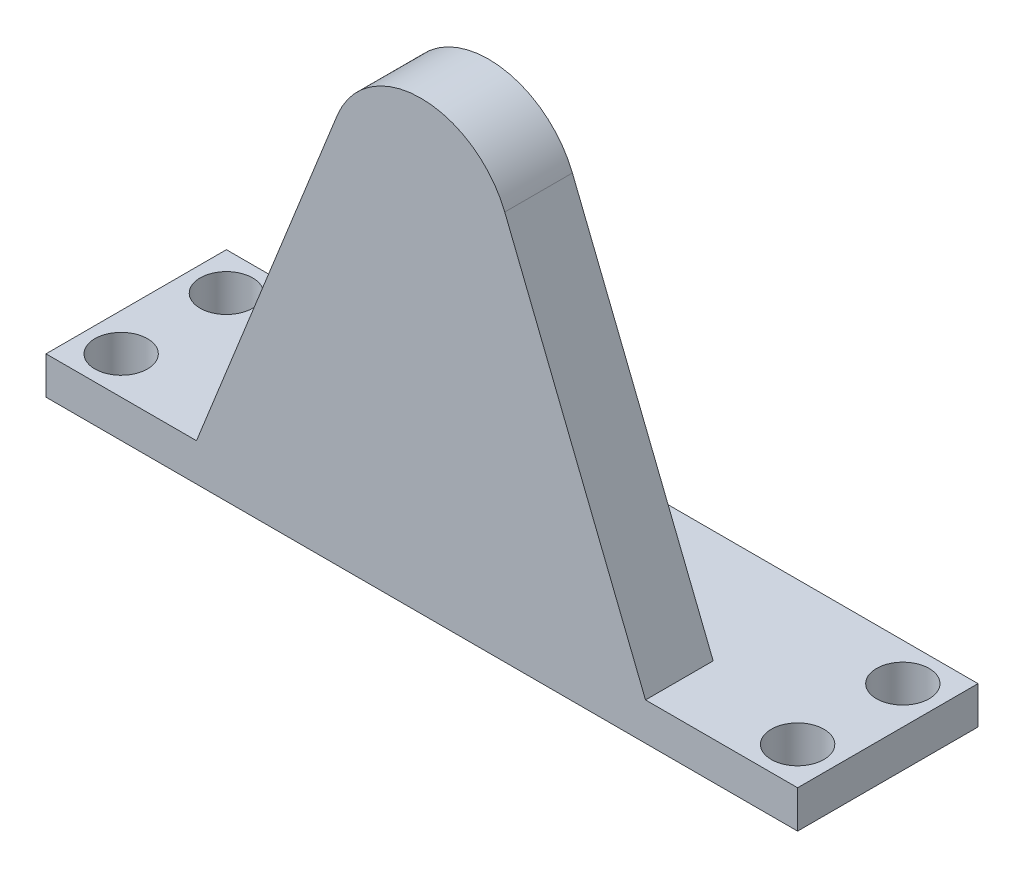
SolidWorks part; units mm, degrees
ref_plane "Front Plane" through (0, 0, 0) normal (0, 0, 1) x (1, 0, 0)
ref_plane "Top Plane" through (0, 0, 0) normal (0, 1, 0) x (1, 0, 0)
ref_plane "Right Plane" through (0, 0, 0) normal (1, 0, 0) x (0, 0, -1)
sketch "Sketch1" plane through (0, 0, 0) normal (0, 1, 0) x (1, 0, 0)
  line L0 (0, 12) -> (0, -12) construction
  line L1 (-50, 12) -> (50, 12)
  line L2 (-50, 12) -> (-50, -12)
  line L3 (-50, -12) -> (50, -12)
  line L4 (50, 12) -> (50, -12)
  line L5 (-45, 0) -> (45, 0) construction
  line L6 (-50, 12) -> (50, -12) construction
  line L7 (-45, 7) -> (-45, -7) construction
  circle A0 centre (-45, 7) radius 3.5
  circle A1 centre (-45, -7) radius 3.5
  circle A2 centre (45, 7) radius 3.5
  circle A3 centre (45, -7) radius 3.5
  dimension "D4" = 90
  dimension "D1" = 100
  dimension "D2" = 24
  dimension "D3" = 45
extrude "Boss-Extrude1" add sketch "Sketch1" along normal blind 5
ref_plane "Plane1" through (0, 0, 3) normal (0, 0, 1) x (1, 0, 0)
sketch "Sketch2" plane through (0, 0, 3) normal (0, 0, 1) x (1, 0, 0)
  line L0 (-50, 5) -> (50, 5) construction
  line L1 (-49.978, 63.276) -> (49.7635, 63.276) construction
  line L2 (-49.978, 63.276) -> (-49.978, 5) construction
  line L3 (-49.978, 5) -> (49.7635, 5) construction
  line L4 (49.7635, 63.276) -> (49.7635, 5) construction
  line L5 (-29.978, 5) -> (29.7635, 5)
  line L6 (-0.1073, 5) -> (-0.1073, 90.7454) construction
  line L7 (-29.978, 5) -> (-11.2501, 51.8549)
  line L8 (11.0356, 51.8549) -> (29.7635, 5)
  arc A0 (11.0356, 51.8549) -> (-11.2501, 51.8549) centre (-0.1073, 47.4011) ccw
  point P13 (-0.1073, 79.733)
  dimension "D3" = 12
  dimension "D1" = 20
  dimension "D2" = 20
extrude "Boss-Extrude2" add sketch "Sketch2" along normal blind 9
sketch "Sketch3" plane through (0, 0, 3) normal (0, 0, -1) x (-1, 0, 0)
  circle A0 centre (0, 49.5783) radius 8
extrude "Cut-Extrude1" cut sketch "Sketch3" against normal blind 4
